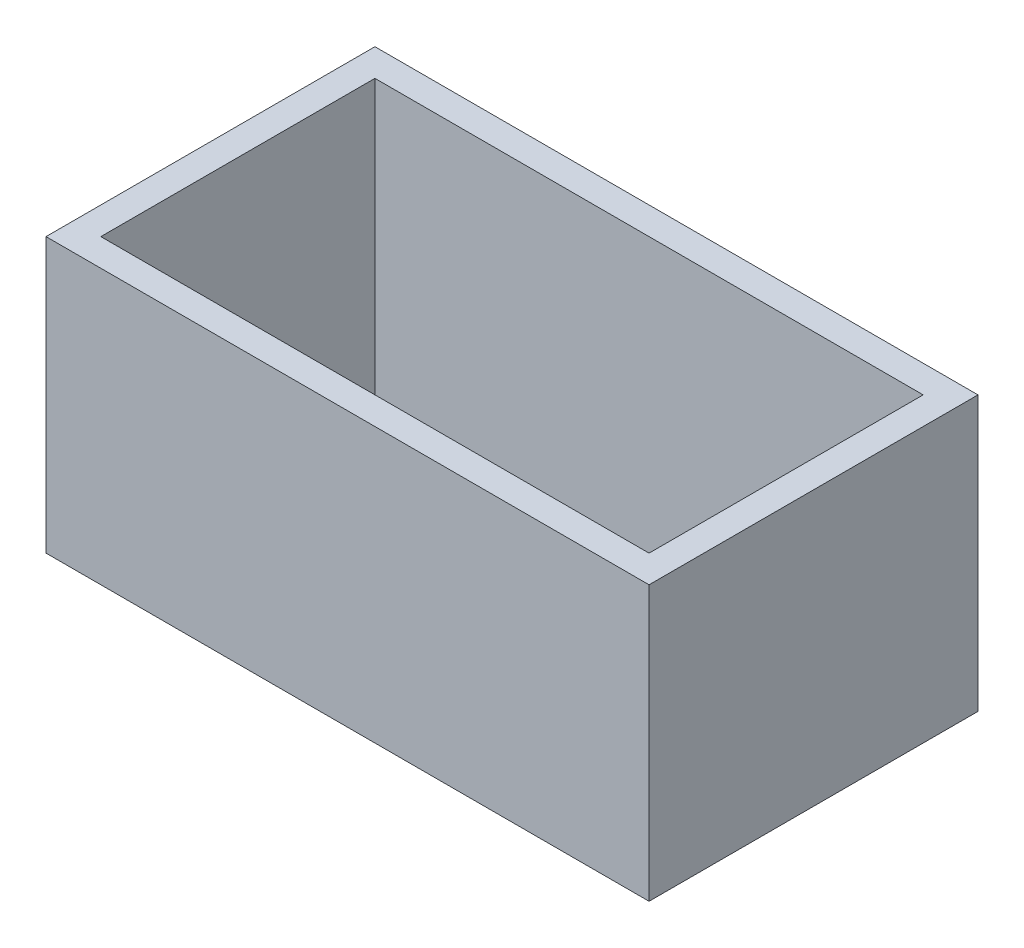
SolidWorks part; units mm, degrees
ref_plane "Front Plane" through (0, 0, 0) normal (0, 0, 1) x (1, 0, 0)
ref_plane "Top Plane" through (0, 0, 0) normal (0, 1, 0) x (1, 0, 0)
ref_plane "Right Plane" through (0, 0, 0) normal (1, 0, 0) x (0, 0, -1)
sketch "Sketch1" plane through (0, 0, 0) normal (0, 1, 0) x (1, 0, 0)
  line L0 (16.5, 9) -> (-16.5, 9)
  line L1 (15, -7.5) -> (-15, -7.5)
  line L2 (15, -7.5) -> (15, 7.5)
  line L3 (15, 7.5) -> (-15, 7.5)
  line L4 (-15, -7.5) -> (-15, 7.5)
  line L5 (15, -7.5) -> (-15, 7.5) construction
  line L6 (15, 7.5) -> (-15, -7.5) construction
  line L7 (-16.5, -9) -> (-16.5, 9)
  line L8 (16.5, -9) -> (-16.5, -9)
  line L9 (16.5, -9) -> (16.5, 9)
  point P0 (0, 0)
  dimension "D1" = 30
  dimension "D2" = 15
  dimension "D3" = 1.5
extrude "Boss-Extrude1" add sketch "Sketch1" along normal blind 15
